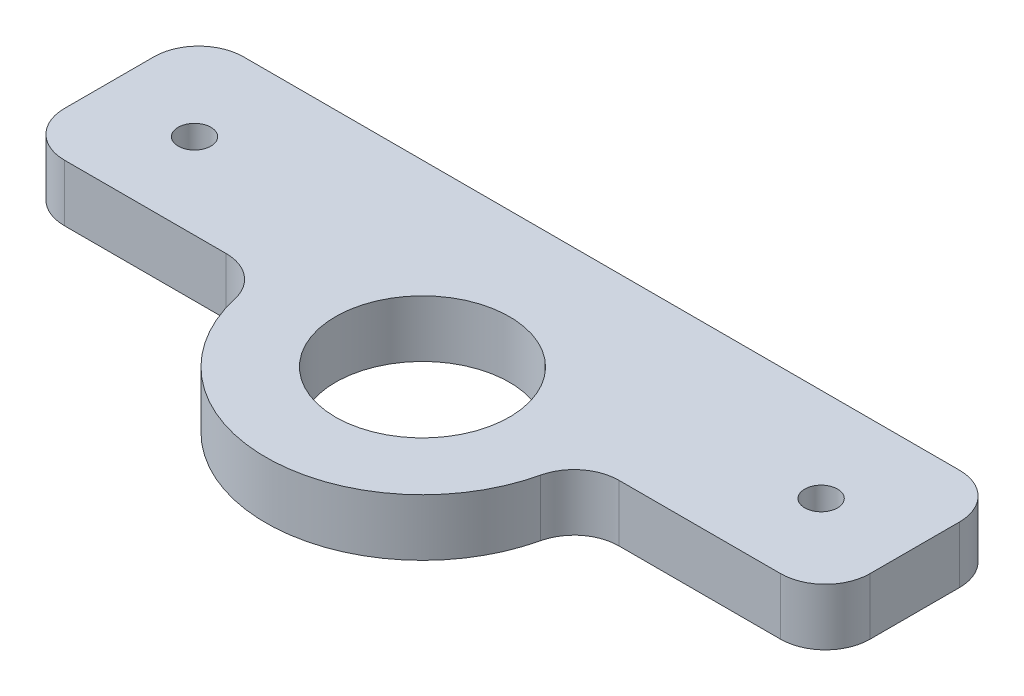
SolidWorks part; units mm, degrees
ref_plane "Front Plane" through (0, 0, 0) normal (0, 0, 1) x (1, 0, 0)
ref_plane "Top Plane" through (0, 0, 0) normal (0, 1, 0) x (1, 0, 0)
ref_plane "Right Plane" through (0, 0, 0) normal (1, 0, 0) x (0, 0, -1)
sketch "Sketch1" plane through (0, 0, 0) normal (0, 1, 0) x (1, 0, 0)
  line L0 (-17.5, -10) -> (-45, -10)
  line L1 (45, -10) -> (17.5, -10)
  line L2 (45, -10) -> (45, 10)
  line L3 (45, 10) -> (-45, 10)
  line L4 (-45, -10) -> (-45, 10)
  line L5 (45, -10) -> (-45, 10) construction
  line L6 (45, 10) -> (-45, -10) construction
  arc A0 (-17.5, -10) -> (17.5, -10) centre (0, -10) ccw
  point P0 (0, 0)
  point P7 (0, 0)
  dimension "D3" = 35
  dimension "D1" = 90
  dimension "D2" = 20
extrude "Boss-Extrude1" add sketch "Sketch1" along normal blind 6.35
hole_wizard "3/4 Clearance Hole1" positions "Sketch2" profile "Sketch3" hole size "3/4" standard "ANSI Inch" end condition through all
sketch "Sketch2" plane through (0, 6.35, 0) normal (0, 1, 0) x (1, 0, 0)
  point P0 (0, -10)
sketch "Sketch3" plane through (0, 6.35, 10) normal (1, 0, 0) x (0, 0, 1)
  line L0 (0, 0) -> (0, 6.35)
  line L1 (0, 6.35) -> (9.7231, 6.35)
  line L2 (9.7231, 6.35) -> (9.7231, 0)
  line L5 (9.7231, 0) -> (0, 0)
  line L11 (0, -6.35) -> (0, 107.95) construction
  dimension "Thru Hole Dia." = 19.4462
  dimension "Thru Hole Depth" = 6.35
fillet "Fillet1" radius 5 6 edges at (45, 3.175, -10) (-45, 3.175, -10) (-45, 3.175, 10) (45, 3.175, 10) (17.5, 3.175, 10) (-17.5, 3.175, 10)
sketch "Sketch4" plane through (0, 6.35, 0) normal (0, 1, 0) x (1, 0, 0)
  line L0 (-35, -0.465) -> (35, -0.465) construction
  line L1 (40, 10) -> (-40, 10) construction
  point P2 (0, -0.465)
  dimension "D1" = 70
  dimension "D2" = 10.465
hole_wizard "#6 Clearance Hole1" positions "Sketch5" profile "Sketch6" hole size "#6" standard "ANSI Inch" end condition through all
sketch "Sketch5" plane through (0, 6.35, 0) normal (0, 1, 0) x (1, 0, 0)
  point P0 (-35, -0.465)
  point P3 (35, -0.465)
sketch "Sketch6" plane through (-35, 6.35, 0.465) normal (1, 0, 0) x (0, 0, 1)
  line L0 (0, 0) -> (0, 6.35)
  line L1 (0, 6.35) -> (1.8288, 6.35)
  line L2 (1.8288, 6.35) -> (1.8288, 0)
  line L5 (1.8288, 0) -> (0, 0)
  line L11 (0, -6.35) -> (0, 107.95) construction
  dimension "Thru Hole Dia." = 3.6576
  dimension "Thru Hole Depth" = 6.35
